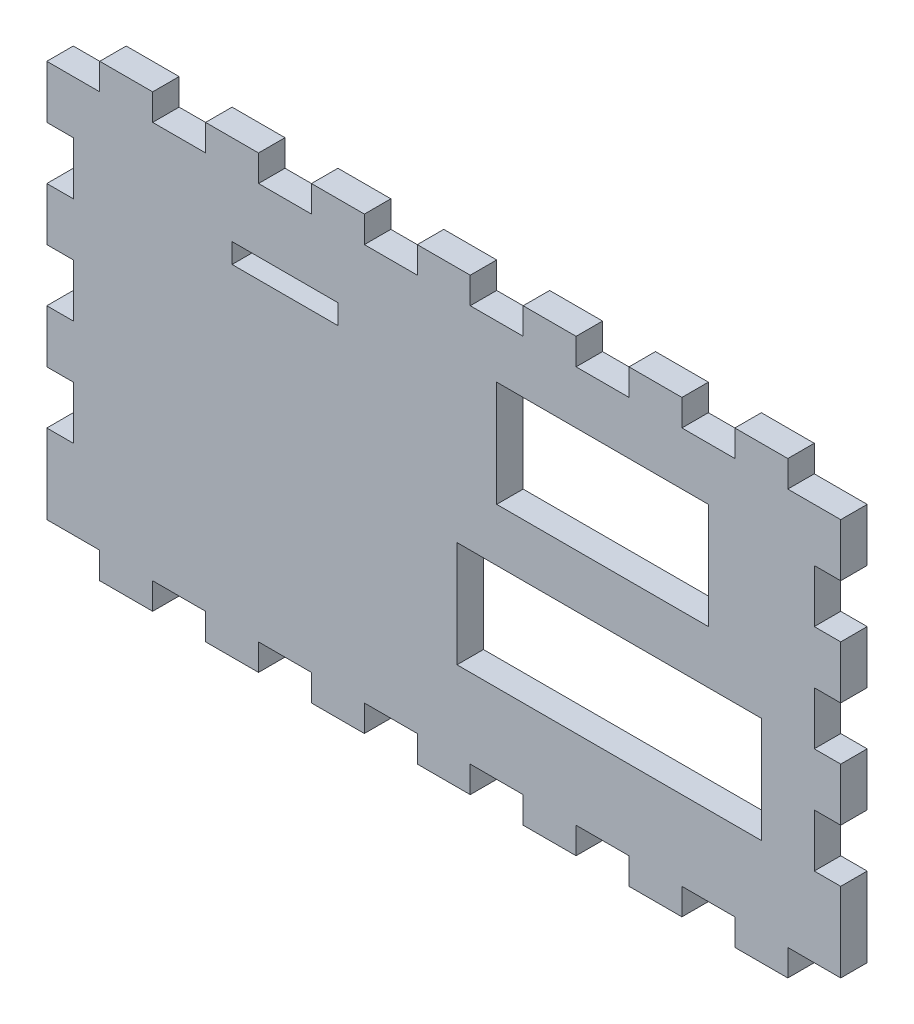
SolidWorks part; units mm, degrees
ref_plane "Front Plane" through (0, 0, 0) normal (0, 0, 1) x (1, 0, 0)
ref_plane "Top Plane" through (0, 0, 0) normal (0, 1, 0) x (1, 0, 0)
ref_plane "Right Plane" through (0, 0, 0) normal (1, 0, 0) x (0, 0, -1)
sketch "Sketch1" plane through (0, 0, 0) normal (0, 0, 1) x (1, 0, 0)
  line L1 (-95.25, 53.975) -> (95.25, 53.975)
  line L2 (-95.25, 53.975) -> (-95.25, -53.975)
  line L3 (-95.25, -53.975) -> (95.25, -53.975)
  line L4 (95.25, 53.975) -> (95.25, -53.975)
  line L5 (-95.25, 53.975) -> (95.25, -53.975) construction
  line L6 (-95.25, -53.975) -> (95.25, 53.975) construction
  point P0 (0, 0)
  dimension "D1" = 107.95
  dimension "D2" = 190.5
extrude "Boss-Extrude1" add sketch "Sketch1" along normal blind 6.35
sketch "Sketch2" plane through (0, 0, 6.35) normal (0, 0, 1) x (1, 0, 0)
  line L1 (-95.25, -53.975) -> (-82.55, -53.975)
  line L2 (-95.25, -53.975) -> (-95.25, -47.625)
  line L3 (-95.25, -47.625) -> (-82.55, -47.625)
  line L4 (-82.55, -53.975) -> (-82.55, -47.625)
  dimension "D1" = 6.35
  dimension "D2" = 12.7
extrude "Cut-Extrude1" cut sketch "Sketch2" against normal through all
pattern_linear "LPattern1" count 8 spacing 25.4 along (1, 0, 0) of "Cut-Extrude1"
mirror "Mirror1" about plane through (0, 0, 0) normal (0, 1, 0) of "LPattern1", "Cut-Extrude1"
sketch "Sketch3" plane through (0, 0, 6.35) normal (0, 0, 1) x (1, 0, 0)
  line L0 (-95.25, 47.625) -> (-95.25, -47.625) construction
  line L1 (-95.25, 34.925) -> (-88.9, 34.925)
  line L2 (-95.25, 34.925) -> (-95.25, 22.225)
  line L3 (-95.25, 22.225) -> (-88.9, 22.225)
  line L4 (-88.9, 34.925) -> (-88.9, 22.225)
  dimension "D1" = 6.35
  dimension "D2" = 12.7
  dimension "D3" = 12.7
extrude "Cut-Extrude2" cut sketch "Sketch3" against normal through all
pattern_linear "LPattern2" count 3 spacing 25.4 along (0, -1, 0) of "Cut-Extrude2"
mirror "Mirror2" about plane through (0, 0, 0) normal (1, 0, 0) of "LPattern2", "Cut-Extrude2"
sketch "Sketch4" plane through (0, 0, 6.35) normal (0, 0, 1) x (1, 0, 0)
  line L0 (-88.9, 22.225) -> (-88.9, 34.925) construction
  line L1 (-50.8, 32.385) -> (-25.4, 32.385)
  line L2 (-50.8, 32.385) -> (-50.8, 27.6225)
  line L3 (-50.8, 27.6225) -> (-25.4, 27.6225)
  line L4 (-25.4, 32.385) -> (-25.4, 27.6225)
  dimension "D1" = 4.7625
  dimension "D2" = 25.4
  dimension "D3" = 15.24
  dimension "D4" = 38.1
extrude "Cut-Extrude3" cut sketch "Sketch4" against normal through all
sketch "Sketch5" plane through (0, 0, 6.35) normal (0, 0, 1) x (1, 0, 0)
  line L0 (88.9, -28.575) -> (88.9, -15.875) construction
  line L1 (3.175, -3.175) -> (76.2, -3.175)
  line L2 (3.175, -3.175) -> (3.175, -28.575)
  line L3 (3.175, -28.575) -> (76.2, -28.575)
  line L4 (76.2, -3.175) -> (76.2, -28.575)
  dimension "D1" = 25.4
  dimension "D2" = 73.025
  dimension "D3" = 19.05
  dimension "D4" = 12.7
extrude "Cut-Extrude4" cut sketch "Sketch5" against normal through all
sketch "Sketch6" plane through (0, 0, 6.35) normal (0, 0, 1) x (1, 0, 0)
  line L1 (12.7, 34.925) -> (63.5, 34.925)
  line L2 (12.7, 34.925) -> (12.7, 9.525)
  line L3 (12.7, 9.525) -> (63.5, 9.525)
  line L4 (63.5, 34.925) -> (63.5, 9.525)
  dimension "D1" = 50.8
  dimension "D2" = 25.4
  dimension "D3" = 25.4
  dimension "D4" = 12.7
extrude "Cut-Extrude5" cut sketch "Sketch6" against normal through all
